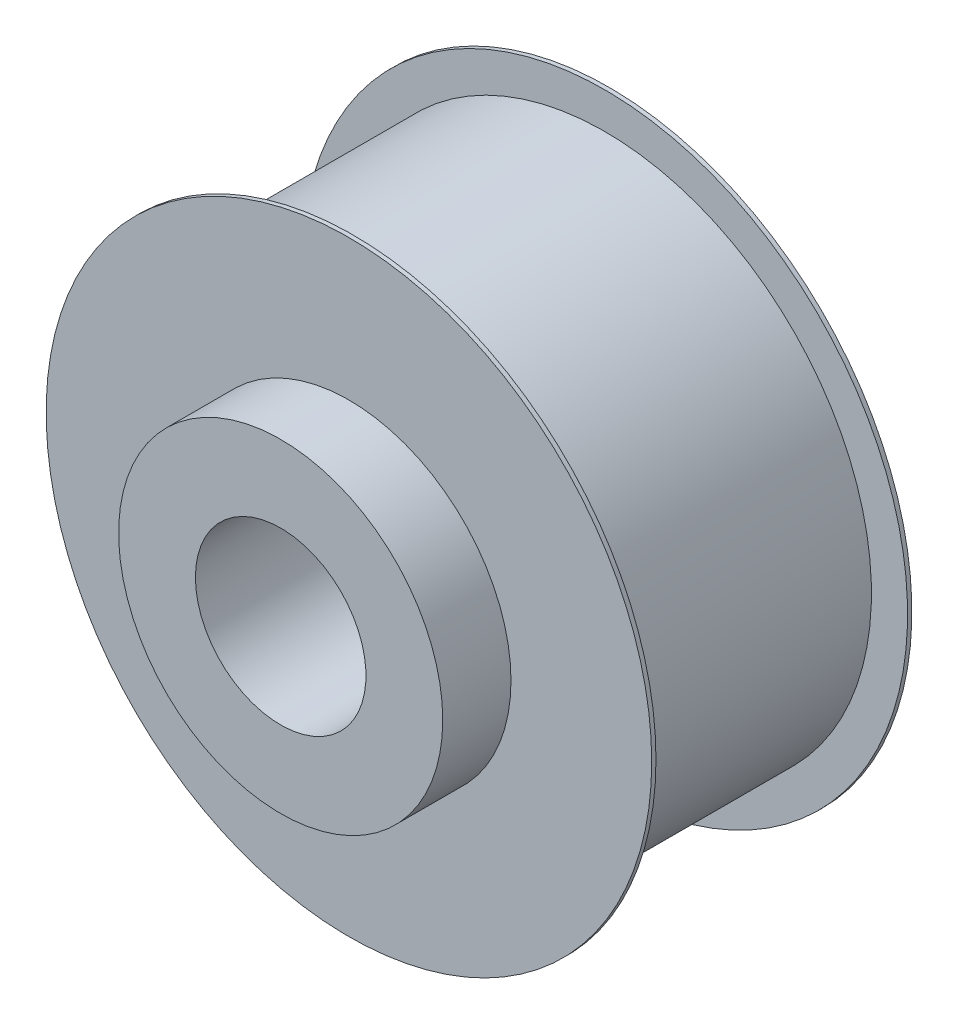
SolidWorks part; units mm, degrees
ref_plane "Płaszczyzna przednia" through (0, 0, 0) normal (0, 0, 1) x (1, 0, 0)
ref_plane "Płaszczyzna górna" through (0, 0, 0) normal (0, 1, 0) x (1, 0, 0)
ref_plane "Płaszczyzna prawa" through (0, 0, 0) normal (1, 0, 0) x (0, 0, -1)
sketch "Szkic1" plane through (0, 0, 0) normal (0, 0, 1) x (1, 0, 0)
  circle A0 centre (0, 0) radius 31.26
  dimension "D1" = 62.52
extrude "Dodanie-wyciągnięcie1" add sketch "Szkic1" along normal blind 30.5
sketch "Szkic2" plane through (0, 0, 30.5) normal (0, 0, 1) x (1, 0, 0)
  circle A0 centre (0, 0) radius 19
  dimension "D1" = 38
extrude "Dodanie-wyciągnięcie2" add sketch "Szkic2" along normal blind 8
sketch "Szkic3" plane through (0, 0, 30.5) normal (0, 0, 1) x (1, 0, 0)
  circle A0 centre (0, 0) radius 35.5
  dimension "D1" = 71
extrude "Dodanie-wyciągnięcie3" add sketch "Szkic3" against normal blind 0.5
sketch "Szkic7" plane through (0, 0, 0) normal (0, 0, -1) x (-1, 0, 0)
  circle A0 centre (0, 0) radius 35.5
  dimension "D1" = 71
extrude "Dodanie-wyciągnięcie4" add sketch "Szkic7" against normal blind 0.5
sketch "Szkic5" plane through (0, 0, 38.5) normal (0, 0, 1) x (1, 0, 0)
  circle A0 centre (0, 0) radius 5
  dimension "D1" = 10
extrude "Wytnij-wyciągnięcie2" [suppressed] cut sketch "Szkic5" against normal through all
sketch "Szkic6" plane through (0, 0, 38.5) normal (0, 0, 1) x (1, 0, 0)
  line L1 (1.5, 0) -> (-1.5, 0)
  line L2 (1.5, 0) -> (1.5, 7)
  line L3 (1.5, 7) -> (-1.5, 7)
  line L4 (-1.5, 0) -> (-1.5, 7)
  line L5 (1.5, 0) -> (-1.5, 7) construction
  line L6 (1.5, 7) -> (-1.5, 0) construction
  point P0 (0, 3.5)
  dimension "D1" = 7
  dimension "D2" = 3
extrude "Wytnij-wyciągnięcie3" [suppressed] cut sketch "Szkic6" against normal blind 40
sketch "Szkic8" plane through (0, 0, 0) normal (0, 0, -1) x (-1, 0, 0)
  circle A0 centre (0, 0) radius 10
  dimension "D1" = 20
extrude "Wytnij-wyciągnięcie4" cut sketch "Szkic8" against normal through all
